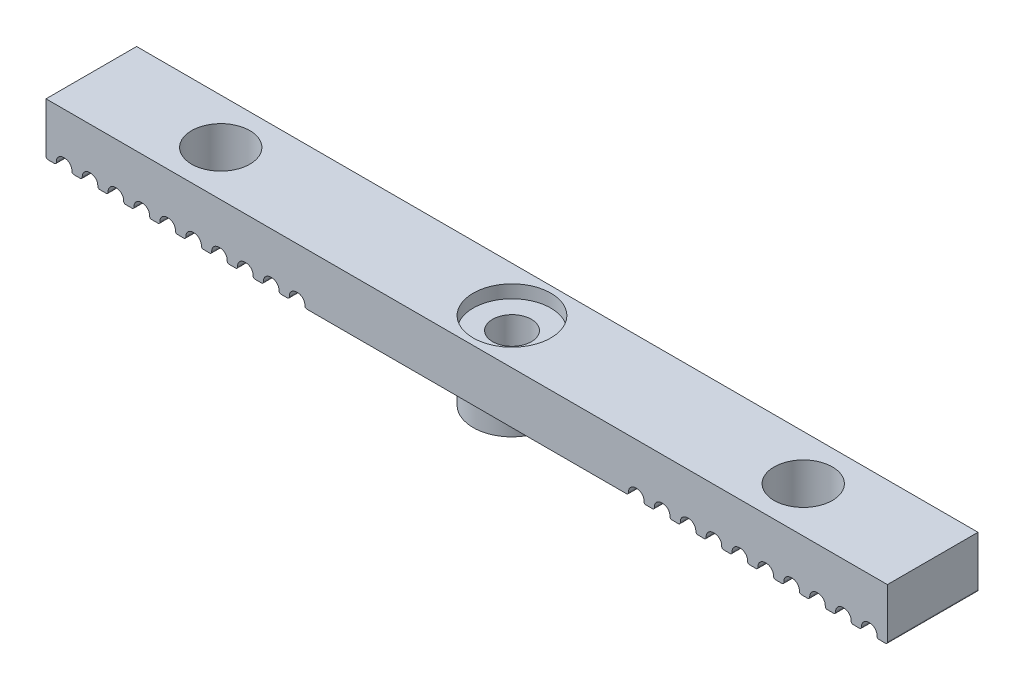
SolidWorks part; units mm, degrees
ref_plane "Front Plane" through (0, 0, 0) normal (0, 0, 1) x (1, 0, 0)
ref_plane "Top Plane" through (0, 0, 0) normal (0, 1, 0) x (1, 0, 0)
ref_plane "Right Plane" through (0, 0, 0) normal (1, 0, 0) x (0, 0, -1)
sketch "Sketch1" plane through (0, 0, 0) normal (0, 1, 0) x (1, 0, 0)
  line L1 (-32.5, 3.5) -> (32.5, 3.5)
  line L2 (-32.5, 3.5) -> (-32.5, -3.5)
  line L3 (-32.5, -3.5) -> (32.5, -3.5)
  line L4 (32.5, 3.5) -> (32.5, -3.5)
  line L5 (0, -3.5) -> (0, 3.5) construction
  line L6 (-32.5, 0) -> (32.5, 0) construction
  point P0 (0, 0)
  dimension "D1" = 65
  dimension "D2" = 7
extrude "Boss-Extrude1" add sketch "Sketch1" along normal blind 4
sketch "Sketch2" plane through (0, 4, 0) normal (0, 1, 0) x (1, 0, 0)
  circle A0 centre (0, 0) radius 1.5
  dimension "D1" = 3
extrude "Cut-Extrude1" cut sketch "Sketch2" against normal up to next
sketch "Sketch3" plane through (0, 4, 0) normal (0, 1, 0) x (1, 0, 0)
  circle A0 centre (0, 0) radius 3
  dimension "D1" = 6
extrude "Cut-Extrude2" cut sketch "Sketch3" against normal blind 1
sketch "Sketch4" plane through (0, 0, 0) normal (0, -1, 0) x (-1, 0, 0)
  circle A0 centre (0, 0) radius 3
  circle A1 centre (0, 0) radius 1.5
  dimension "D1" = 6
extrude "Boss-Extrude2" add sketch "Sketch4" along normal blind 2
sketch "Sketch5" plane through (0, 0, -3.5) normal (0, 0, -1) x (-1, 0, 0)
  line L0 (32.5, 0) -> (12.5, 0) construction
  line L1 (-32.5, 0) -> (32.5, 0) construction
  line L2 (-32.5, 0) -> (-12.5, 0) construction
  line L3 (32.5, 0) -> (31.7, 0)
  line L4 (31.7, 0) -> (31.7, 0.75)
  line L5 (31.7, 0.75) -> (30.5, 0.75)
  line L6 (32.5, 0) -> (32.5, 0.75)
  line L7 (32.5, 4) -> (32.5, 0) construction
  line L8 (30.5, 0) -> (30.5, 0.75)
  line L9 (30.5, 0) -> (29.7, 0)
  line L10 (29.7, 0) -> (29.7, 0.75)
  line L11 (29.7, 0.75) -> (28.5, 0.75)
  line L12 (28.5, 0) -> (28.5, 0.75)
  line L13 (28.5, 0) -> (27.7, 0)
  line L14 (27.7, 0) -> (27.7, 0.75)
  line L15 (27.7, 0.75) -> (26.5, 0.75)
  line L16 (26.5, 0) -> (26.5, 0.75)
  line L17 (26.5, 0) -> (25.7, 0)
  line L18 (25.7, 0) -> (25.7, 0.75)
  line L19 (25.7, 0.75) -> (24.5, 0.75)
  line L20 (24.5, 0) -> (24.5, 0.75)
  line L21 (24.5, 0) -> (23.7, 0)
  line L22 (23.7, 0) -> (23.7, 0.75)
  line L23 (23.7, 0.75) -> (22.5, 0.75)
  line L24 (22.5, 0) -> (22.5, 0.75)
  line L25 (22.5, 0) -> (21.7, 0)
  line L26 (21.7, 0) -> (21.7, 0.75)
  line L27 (21.7, 0.75) -> (20.5, 0.75)
  line L28 (20.5, 0) -> (20.5, 0.75)
  line L29 (20.5, 0) -> (19.7, 0)
  line L30 (19.7, 0) -> (19.7, 0.75)
  line L31 (19.7, 0.75) -> (18.5, 0.75)
  line L32 (18.5, 0) -> (18.5, 0.75)
  line L33 (18.5, 0) -> (17.7, 0)
  line L34 (17.7, 0) -> (17.7, 0.75)
  line L35 (17.7, 0.75) -> (16.5, 0.75)
  line L36 (16.5, 0) -> (16.5, 0.75)
  line L37 (16.5, 0) -> (15.7, 0)
  line L38 (15.7, 0) -> (15.7, 0.75)
  line L39 (15.7, 0.75) -> (14.5, 0.75)
  line L40 (14.5, 0) -> (14.5, 0.75)
  line L41 (14.5, 0) -> (13.7, 0)
  line L42 (13.7, 0) -> (13.7, 0.75)
  line L43 (13.7, 0.75) -> (12.5, 0.75)
  line L44 (-32.5, 0.75) -> (-32.5, 0)
  line L45 (-32.5, 4) -> (-32.5, 0) construction
  line L46 (-32.5, 0) -> (-31.7, 0)
  line L47 (-31.7, 0) -> (-31.7, 0.75)
  line L48 (-31.7, 0.75) -> (-30.5, 0.75)
  line L49 (-30.5, 0.75) -> (-30.5, 0)
  line L50 (-30.5, 0) -> (-29.7, 0)
  line L51 (-29.7, 0) -> (-29.7, 0.75)
  line L52 (-29.7, 0.75) -> (-28.5, 0.75)
  line L53 (-28.5, 0.75) -> (-28.5, 0)
  line L54 (-28.5, 0) -> (-27.7, 0)
  line L55 (-27.7, 0) -> (-27.7, 0.75)
  line L56 (-27.7, 0.75) -> (-26.5, 0.75)
  line L57 (-26.5, 0.75) -> (-26.5, 0)
  line L58 (-26.5, 0) -> (-25.7, 0)
  line L59 (-25.7, 0) -> (-25.7, 0.75)
  line L60 (-25.7, 0.75) -> (-24.5, 0.75)
  line L61 (-24.5, 0.75) -> (-24.5, 0)
  line L62 (-24.5, 0) -> (-23.7, 0)
  line L63 (-23.7, 0) -> (-23.7, 0.75)
  line L64 (-23.7, 0.75) -> (-22.5, 0.75)
  line L65 (-22.5, 0.75) -> (-22.5, 0)
  line L66 (-22.5, 0) -> (-21.7, 0)
  line L67 (-21.7, 0) -> (-21.7, 0.75)
  line L68 (-21.7, 0.75) -> (-20.5, 0.75)
  line L69 (-20.5, 0.75) -> (-20.5, 0)
  line L70 (-20.5, 0) -> (-19.7, 0)
  line L71 (-19.7, 0) -> (-19.7, 0.75)
  line L72 (-19.7, 0.75) -> (-18.5, 0.75)
  line L73 (-18.5, 0.75) -> (-18.5, 0)
  line L74 (-18.5, 0) -> (-17.7, 0)
  line L75 (-17.7, 0) -> (-17.7, 0.75)
  line L76 (-17.7, 0.75) -> (-16.5, 0.75)
  line L77 (-16.5, 0.75) -> (-16.5, 0)
  line L78 (-16.5, 0) -> (-15.7, 0)
  line L79 (-15.7, 0) -> (-15.7, 0.75)
  line L80 (-15.7, 0.75) -> (-14.5, 0.75)
  line L81 (-14.5, 0.75) -> (-14.5, 0)
  line L82 (-14.5, 0) -> (-13.7, 0)
  line L83 (-13.7, 0) -> (-13.7, 0.75)
  line L84 (-13.7, 0.75) -> (-12.5, 0.75)
  line L85 (-12.5, 0) -> (-12.5, 0.75)
  line L86 (12.5, 0) -> (12.5, 0.75)
  line M46 (-32.5, 0) -> (32.5, 0)
  dimension "D1" = 20
  dimension "D2" = 20
  dimension "D3" = 0.8
  dimension "D4" = 0.75
  dimension "D5" = 1.2
  dimension "D7" = 0.8
  dimension "D8" = 1.2
  dimension "D9" = 0.75
  dimension "D6" = 10
  dimension "D10" = 10
extrude "Cut-Extrude3" cut sketch "Sketch5" against normal through all contours L8 L4 L5 M46 | L12 L10 L11 M46 | L16 L14 L15 M46 | L20 L18 L19 M46 | L24 L22 L23 M46 | L28 L26 L27 M46 | L32 L30 L31 M46 | L36 L34 L35 M46 | L40 L38 L39 M46 | L86 L42 L43 M46 | L49 L48 L47 M46 | L53 L52 L51 M46 | L57 L56 L55 M46 | L61 L60 L59 M46 | L65 L64 L63 M46 | L69 L68 L67 M46 | L73 L72 L71 M46 | L77 L76 L75 M46 | L81 L80 L79 M46 | L85 L84 L83 M46
fillet "Fillet1" radius 0.15 42 edges at (32.5, 0, 0) (31.7, 0, 0) (30.5, 0, 0) (29.7, 0, 0) (28.5, 0, 0) (27.7, 0, 0) (26.5, 0, 0) (25.7, 0, 0) (23.7, 0, 0) (24.5, 0, 0) (22.5, 0, 0) (21.7, 0, 0) (20.5, 0, 0) (19.7, 0, 0) (18.5, 0, 0) (17.7, 0, 0) (16.5, 0, 0) (15.7, 0, 0) (14.5, 0, 0) (13.7, 0, 0) (12.5, 0, 0) (-12.5, 0, 0) (-13.7, 0, 0) (-14.5, 0, 0) (-16.5, 0, 0) (-15.7, 0, 0) (-17.7, 0, 0) (-18.5, 0, 0) (-20.5, 0, 0) (-21.7, 0, 0) (-22.5, 0, 0) (-23.7, 0, 0) (-24.5, 0, 0) (-26.5, 0, 0) (-27.7, 0, 0) (-28.5, 0, 0) (-29.7, 0, 0) (-30.5, 0, 0) (-31.7, 0, 0) (-32.5, 0, 0) (-19.7, 0, 0) (-25.7, 0, 0)
fillet "Fillet2" radius 0.555 40 edges at (30.5, 0.75, 0) (28.5, 0.75, 0) (26.5, 0.75, 0) (27.7, 0.75, 0) (29.7, 0.75, 0) (31.7, 0.75, 0) (25.7, 0.75, 0) (24.5, 0.75, 0) (23.7, 0.75, 0) (22.5, 0.75, 0) (21.7, 0.75, 0) (20.5, 0.75, 0) (19.7, 0.75, 0) (18.5, 0.75, 0) (17.7, 0.75, 0) (16.5, 0.75, 0) (15.7, 0.75, 0) (14.5, 0.75, 0) (13.7, 0.75, 0) (12.5, 0.75, 0) (-12.5, 0.75, 0) (-13.7, 0.75, 0) (-14.5, 0.75, 0) (-15.7, 0.75, 0) (-16.5, 0.75, 0) (-17.7, 0.75, 0) (-18.5, 0.75, 0) (-19.7, 0.75, 0) (-20.5, 0.75, 0) (-21.7, 0.75, 0) (-22.5, 0.75, 0) (-23.7, 0.75, 0) (-24.5, 0.75, 0) (-25.7, 0.75, 0) (-26.5, 0.75, 0) (-27.7, 0.75, 0) (-28.5, 0.75, 0) (-29.7, 0.75, 0) (-30.5, 0.75, 0) (-31.7, 0.75, 0)
sketch "Sketch6" plane through (0, 4, 0) normal (0, 1, 0) x (1, 0, 0)
  line L0 (-32.5, 3.5) -> (-32.5, -3.5) construction
  line L1 (32.5, -3.5) -> (32.5, 3.5) construction
  circle A0 centre (-22.5, 0) radius 2.25
  circle A1 centre (22.5, 0) radius 2.25
  point P6 (-32.5, 0)
  point P9 (32.5, 0)
  dimension "D1" = 4.5
  dimension "D2" = 4.5
  dimension "D3" = 10
  dimension "D4" = 10
extrude "Cut-Extrude4" cut sketch "Sketch6" against normal through all
